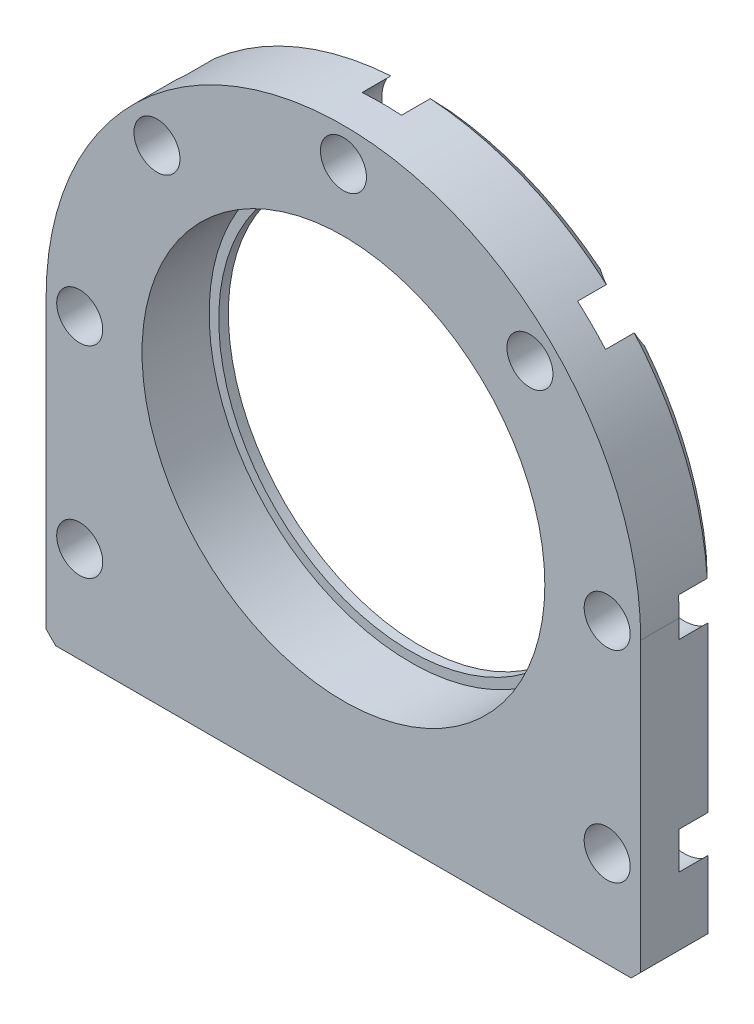
SolidWorks part; units mm, degrees
material "ABS"
ref_plane "正面" through (0, 0, 0) normal (0, 0, 1) x (1, 0, 0)
ref_plane "平面" through (0, 0, 0) normal (0, 1, 0) x (1, 0, 0)
ref_plane "右側面" through (0, 0, 0) normal (1, 0, 0) x (0, 0, -1)
sketch "ｽｹｯﾁ1" plane through (0, 0, 0) normal (0, 0, 1) x (1, 0, 0)
  line L0 (0, 0) -> (0, -31) construction
  line L1 (31, -31) -> (-31, -31)
  line L2 (-31, 0) -> (-31, -31)
  line L3 (31, 0) -> (31, -31)
  circle A0 centre (0, 0) radius 31 construction
  arc A1 (-31, 0) -> (31, 0) centre (0, 0) cw
  point P8 (0, -31)
  dimension "D1" = 62
extrude "ﾎﾞｽ - 押し出し1" add sketch "ｽｹｯﾁ1" along normal blind 8
sketch "ｽｹｯﾁ2" plane through (0, 0, 8) normal (0, 0, 1) x (1, 0, 0)
  circle A0 centre (0, 0) radius 24
  dimension "D1" = 48
extrude "ｶｯﾄ - 押し出し1" [suppressed] cut sketch "ｽｹｯﾁ2" against normal through all
chamfer "面取り1" distance 1 angle 45 6 edges at (-31, -15.5, 0) (0, 31, 0) (31, -15.5, 0) (31, -31, 4) (0, -31, 0) (-31, -31, 4)
hole_wizard "M4 穴付きねじ用座ぐり穴1" positions "ｽｹｯﾁ3" profile "ｽｹｯﾁ4" counterbore size "M4" standard "JIS" end condition through all
sketch "ｽｹｯﾁ3" plane through (0, 0, 0) normal (0, 0, 1) x (1, 0, 0)
  point P0 (0, 27.5)
  dimension "D1" = 27.5
sketch "ｽｹｯﾁ4" plane through (0, 27.5, 0) normal (1, 0, 0) x (0, 1, 0)
  line L0 (0, 0) -> (0, 8)
  line L1 (0, 8) -> (2.4, 8)
  line L3 (2.4, 8) -> (2.4, 4)
  line L4 (2.4, 4) -> (4, 4)
  line L5 (4, 4) -> (4, 0)
  line L7 (4, 0) -> (0, 0)
  line L11 (0, -6.35) -> (0, 107.95) construction
  dimension "通し穴の直径" = 4.8
  dimension "通し穴の深さ" = 8
  dimension "座ぐり穴の直径" = 8
  dimension "座ぐり穴の深さ" = 4
pattern_circular "円形ﾊﾟﾀｰﾝ1" count 8 over 360 about axis through (0, 0, 0) along (0, 0, 1) skipping 3, 4, 5 of "M4 穴付きねじ用座ぐり穴1"
sketch "ｽｹｯﾁ11" plane through (0, 0, 8) normal (0, 0, 1) x (1, 0, 0)
  circle A0 centre (0, 0) radius 21
  dimension "D1" = 42
extrude "ｶｯﾄ - 押し出し8" cut sketch "ｽｹｯﾁ11" against normal blind 7
sketch "ｽｹｯﾁ12" plane through (0, 0, 1) normal (0, 0, 1) x (1, 0, 0)
  circle A0 centre (0, 0) radius 20
  dimension "D1" = 40
extrude "ｶｯﾄ - 押し出し9" cut sketch "ｽｹｯﾁ12" against normal through all
hole_wizard "M4 穴付きねじ用座ぐり穴2" positions "ｽｹｯﾁ13" profile "ｽｹｯﾁ14" counterbore size "M4" standard "JIS" end condition through all
sketch "ｽｹｯﾁ13" plane through (0, 0, 0) normal (0, 0, -1) x (-1, 0, 0)
  line L0 (0, 0) -> (0, -31) construction
  line L1 (30, -31) -> (-30, -31) construction
  line L7 (-27.5, -21) -> (27.5, -21) construction
  line L10 (-27.5, 0) -> (-27.5, -21) construction
  point P17 (-27.5, -21)
  point P18 (27.5, -21)
  dimension "D1" = 10
sketch "ｽｹｯﾁ14" plane through (-27.5, -21, 0) normal (1, 0, 0) x (0, 1, 0)
  line L0 (0, 0) -> (0, 8)
  line L1 (0, 8) -> (2.4, 8)
  line L3 (2.4, 8) -> (2.4, 4)
  line L4 (2.4, 4) -> (4, 4)
  line L5 (4, 4) -> (4, 0)
  line L7 (4, 0) -> (0, 0)
  line L11 (0, -6.35) -> (0, 107.95) construction
  dimension "通し穴の直径" = 4.8
  dimension "通し穴の深さ" = 8
  dimension "座ぐり穴の直径" = 8
  dimension "座ぐり穴の深さ" = 4
